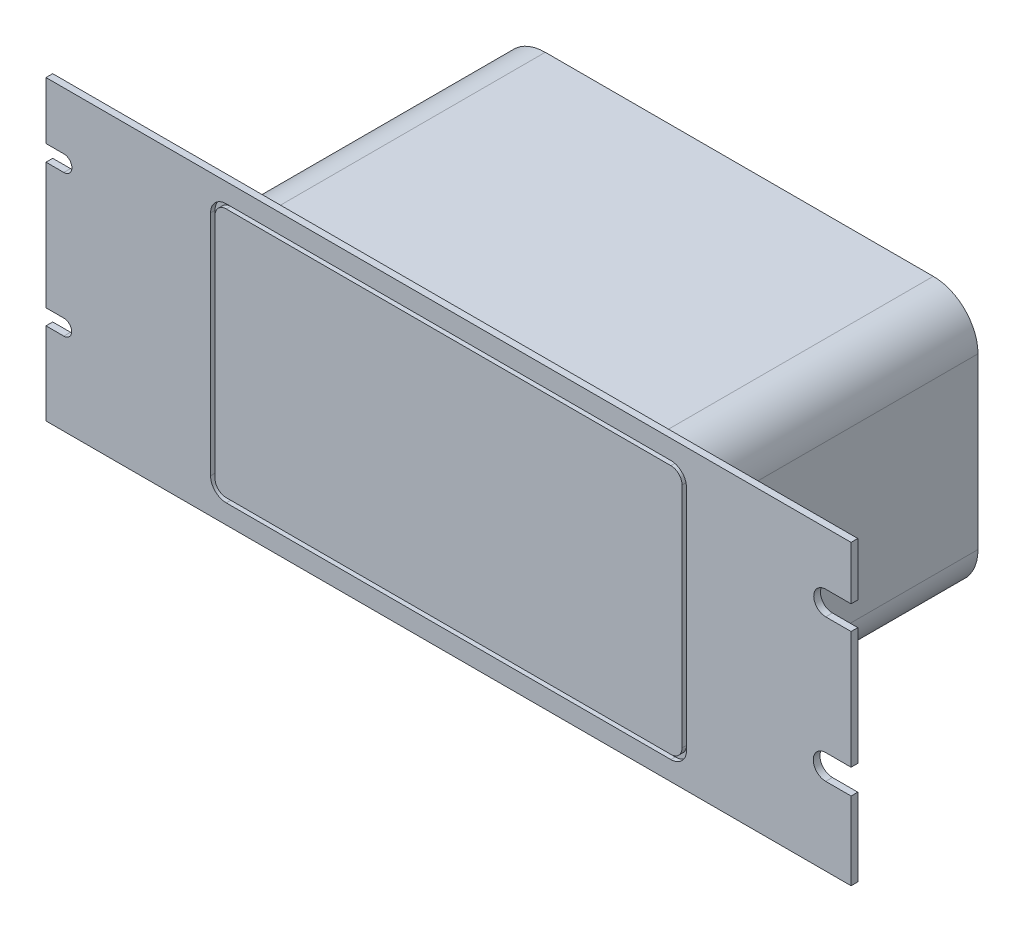
SolidWorks part; units mm, degrees
ref_plane "Alzado" through (0, 0, 0) normal (0, 0, 1) x (1, 0, 0)
ref_plane "Planta" through (0, 0, 0) normal (0, 1, 0) x (1, 0, 0)
ref_plane "Vista lateral" through (0, 0, 0) normal (1, 0, 0) x (0, 0, -1)
sketch "Croquis1" plane through (0, 0, 0) normal (0, 0, 1) x (1, 0, 0)
  line L0 (-180, 59.5) -> (-180, 66.5)
  line L1 (-173, -66.5) -> (173, -66.5)
  line L2 (-180, -59.5) -> (-180, 59.5)
  line L3 (-173, 66.5) -> (173, 66.5)
  line L4 (180, -59.5) -> (180, 59.5)
  line L5 (-180, -66.5) -> (180, 66.5) construction
  line L6 (-180, 66.5) -> (180, -66.5) construction
  line L7 (-86.753, 57.9006) -> (86.753, 57.9006)
  line L8 (-106.753, 37.9006) -> (-106.753, -37.9006)
  line L9 (-86.753, -57.9006) -> (86.753, -57.9006)
  line L10 (106.753, 37.9006) -> (106.753, -37.9006)
  line L11 (-106.753, 57.9006) -> (106.753, -57.9006) construction
  line L12 (-106.753, -57.9006) -> (106.753, 57.9006) construction
  line L13 (-180, 66.5) -> (-173, 66.5)
  line L14 (-180, -59.5) -> (-180, -66.5)
  line L15 (-180, -66.5) -> (-173, -66.5)
  line L16 (173, -66.5) -> (180, -66.5)
  line L17 (180, -66.5) -> (180, -59.5)
  line L18 (173, 66.5) -> (180, 66.5)
  line L19 (180, 66.5) -> (180, 59.5)
  arc A0 (86.753, 57.9006) -> (106.753, 37.9006) centre (86.753, 37.9006) cw
  arc A1 (86.753, -57.9006) -> (106.753, -37.9006) centre (86.753, -37.9006) ccw
  arc A2 (-106.753, -37.9006) -> (-86.753, -57.9006) centre (-86.753, -37.9006) ccw
  arc A3 (-86.753, 57.9006) -> (-106.753, 37.9006) centre (-86.753, 37.9006) ccw
  point P0 (0, 0)
  point P6 (0, 0)
  dimension "D3" = 20
  dimension "D1" = 133
  dimension "D2" = 360
extrude "Saliente-Extruir1" add sketch "Croquis1" along normal blind 3
sketch "Croquis2" plane through (0, 0, 3) normal (0, 0, 1) x (1, 0, 0)
  line L0 (-106.753, 37.9006) -> (-106.753, -37.9006)
  line L1 (-86.753, -57.9006) -> (86.753, -57.9006)
  line L2 (106.753, -37.9006) -> (106.753, 37.9006)
  line L3 (86.753, 57.9006) -> (-86.753, 57.9006)
  arc A0 (-106.753, -37.9006) -> (-86.753, -57.9006) centre (-86.753, -37.9006) ccw
  arc A1 (86.753, -57.9006) -> (106.753, -37.9006) centre (86.753, -37.9006) ccw
  arc A2 (106.753, 37.9006) -> (86.753, 57.9006) centre (86.753, 37.9006) ccw
  arc A3 (-86.753, 57.9006) -> (-106.753, 37.9006) centre (-86.753, 37.9006) ccw
extrude "Saliente-Extruir2" add sketch "Croquis2" against normal blind 130
sketch "Croquis3" plane through (0, 0, 3) normal (0, 0, 1) x (1, 0, 0)
  line L0 (-104.4129, -50.9098) -> (-104.4129, 50.9098)
  line L1 (99.4129, -57.9098) -> (-99.4129, -57.9098)
  line L2 (106.4129, -50.9098) -> (106.4129, 50.9098)
  line L3 (99.4129, 57.9098) -> (-99.4129, 57.9098)
  line L4 (-106.4129, -50.9098) -> (-106.4129, 50.9098)
  line L5 (106.4129, -57.9098) -> (-106.4129, 57.9098) construction
  line L6 (106.4129, 57.9098) -> (-106.4129, -57.9098) construction
  line L7 (99.4129, 55.9098) -> (-99.4129, 55.9098)
  line L8 (104.4129, -50.9098) -> (104.4129, 50.9098)
  line L9 (99.4129, -55.9098) -> (-99.4129, -55.9098)
  arc A0 (-99.4129, 57.9098) -> (-106.4129, 50.9098) centre (-99.4129, 50.9098) ccw
  arc A1 (-99.4129, -57.9098) -> (-106.4129, -50.9098) centre (-99.4129, -50.9098) cw
  arc A2 (99.4129, -57.9098) -> (106.4129, -50.9098) centre (99.4129, -50.9098) ccw
  arc A3 (106.4129, 50.9098) -> (99.4129, 57.9098) centre (99.4129, 50.9098) ccw
  arc A4 (-99.4129, 55.9098) -> (-104.4129, 50.9098) centre (-99.4129, 50.9098) ccw
  arc A5 (104.4129, 50.9098) -> (99.4129, 55.9098) centre (99.4129, 50.9098) ccw
  arc A6 (99.4129, -55.9098) -> (104.4129, -50.9098) centre (99.4129, -50.9098) ccw
  arc A7 (-99.4129, -55.9098) -> (-104.4129, -50.9098) centre (-99.4129, -50.9098) cw
  point P0 (0, 0)
  dimension "D1" = 7
  dimension "D2" = 2
extrude "Cortar-Extruir1" cut sketch "Croquis3" against normal blind 2
sketch "Croquis4" plane through (0, 0, 3) normal (0, 0, 1) x (1, 0, 0)
  line L0 (-180, 37.3327) -> (180, 37.3327) construction
  line L1 (-180, 66.5) -> (-180, -66.5) construction
  line L2 (180, -66.5) -> (180, 66.5) construction
  line L3 (-180, -26.1623) -> (180, -26.1623) construction
  line L4 (-180, 37.3327) -> (-172.017, 37.3327) construction
  line L5 (-180, 40.9366) -> (-172.017, 40.9366)
  line L6 (-180, 33.7288) -> (-172.017, 33.7288)
  line L7 (-180, -26.1623) -> (-172.017, -26.1623) construction
  line L8 (-180, -22.6789) -> (-172.017, -22.6789)
  line L9 (-180, -29.6457) -> (-172.017, -29.6457)
  line L10 (180, 37.3327) -> (168.6559, 37.3327) construction
  line L11 (180, 31.9768) -> (168.6559, 31.9768)
  line L12 (180, 42.6887) -> (168.6559, 42.6887)
  line L13 (180, -26.1623) -> (168.6559, -26.1623) construction
  line L14 (180, -31.7314) -> (168.6559, -31.7314)
  line L15 (180, -20.5932) -> (168.6559, -20.5932)
  arc A0 (-180, 40.9366) -> (-180, 33.7288) centre (-180, 37.3327) ccw
  arc A1 (-172.017, 33.7288) -> (-172.017, 40.9366) centre (-172.017, 37.3327) ccw
  arc A2 (-180, -22.6789) -> (-180, -29.6457) centre (-180, -26.1623) ccw
  arc A3 (-172.017, -29.6457) -> (-172.017, -22.6789) centre (-172.017, -26.1623) ccw
  arc A4 (180, 31.9768) -> (180, 42.6887) centre (180, 37.3327) ccw
  arc A5 (168.6559, 42.6887) -> (168.6559, 31.9768) centre (168.6559, 37.3327) ccw
  arc A6 (180, -31.7314) -> (180, -20.5932) centre (180, -26.1623) ccw
  arc A7 (168.6559, -20.5932) -> (168.6559, -31.7314) centre (168.6559, -26.1623) ccw
  point P8 (-176.0085, 37.3327)
  point P14 (-176.0085, -26.1623)
  point P20 (174.3279, 37.3327)
  point P26 (174.3279, -26.1623)
extrude "Cortar-Extruir2" cut sketch "Croquis4" against normal blind 29
